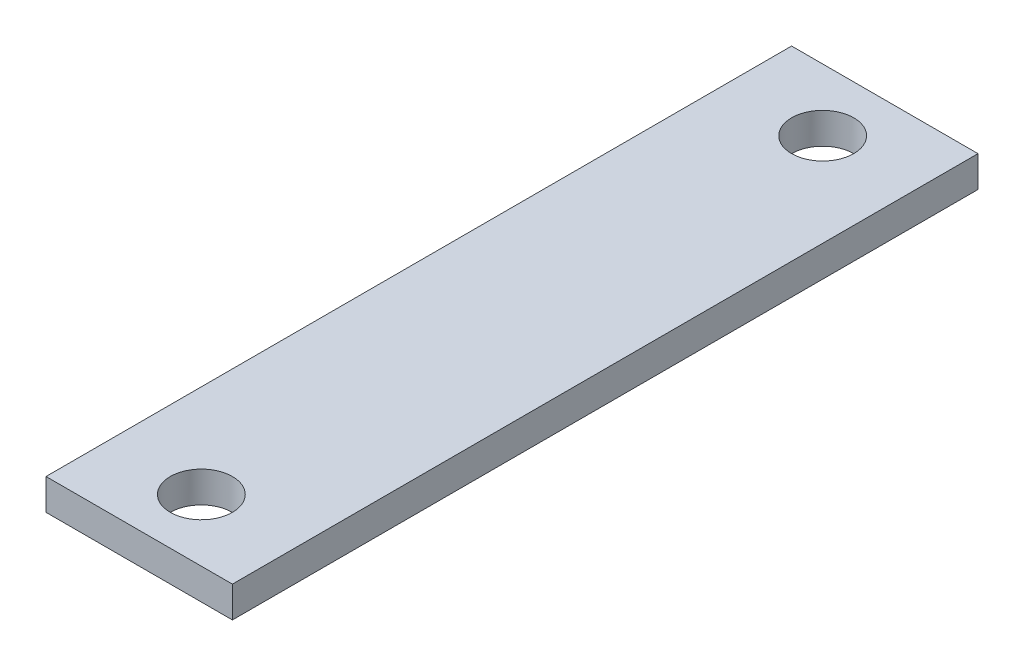
SolidWorks part; units mm, degrees
ref_plane "Front" through (0, 0, 0) normal (0, 0, 1) x (1, 0, 0)
ref_plane "Top" through (0, 0, 0) normal (0, 1, 0) x (1, 0, 0)
ref_plane "Right" through (0, 0, 0) normal (1, 0, 0) x (0, 0, -1)
sketch "Sketch1" plane through (0, 0, 0) normal (0, 1, 0) x (1, 0, 0)
  line L1 (-1.5, -3.2318) -> (1.5, -3.2318)
  line L2 (-1.5, -3.2318) -> (-1.5, 8.7682)
  line L3 (-1.5, 8.7682) -> (1.5, 8.7682)
  line L4 (1.5, -3.2318) -> (1.5, 8.7682)
  line L5 (-1.5, -3.2318) -> (1.5, 8.7682) construction
  line L6 (-1.5, 8.7682) -> (1.5, -3.2318) construction
  point P0 (0, 0)
  point P5 (0, 0)
  point P6 (0, 0)
  dimension "D1" = 3
  dimension "D2" = 12
extrude "Boss-Extrude1" add sketch "Sketch1" along normal blind 0.5
sketch "Sketch2" plane through (0, 0.5, 0) normal (0, 1, 0) x (1, 0, 0)
  line L0 (-1.5, -3.2318) -> (1.5, -3.2318) construction
  line L1 (1.5, 8.7682) -> (-1.5, 8.7682) construction
  circle A0 centre (0, 7.7682) radius 0.5
  circle A1 centre (0, -2.2318) radius 0.5
  dimension "D1" = 1
  dimension "D2" = 1
  dimension "D3" = 1
  dimension "D4" = 1
extrude "Cut-Extrude1" cut sketch "Sketch2" against normal blind 1
